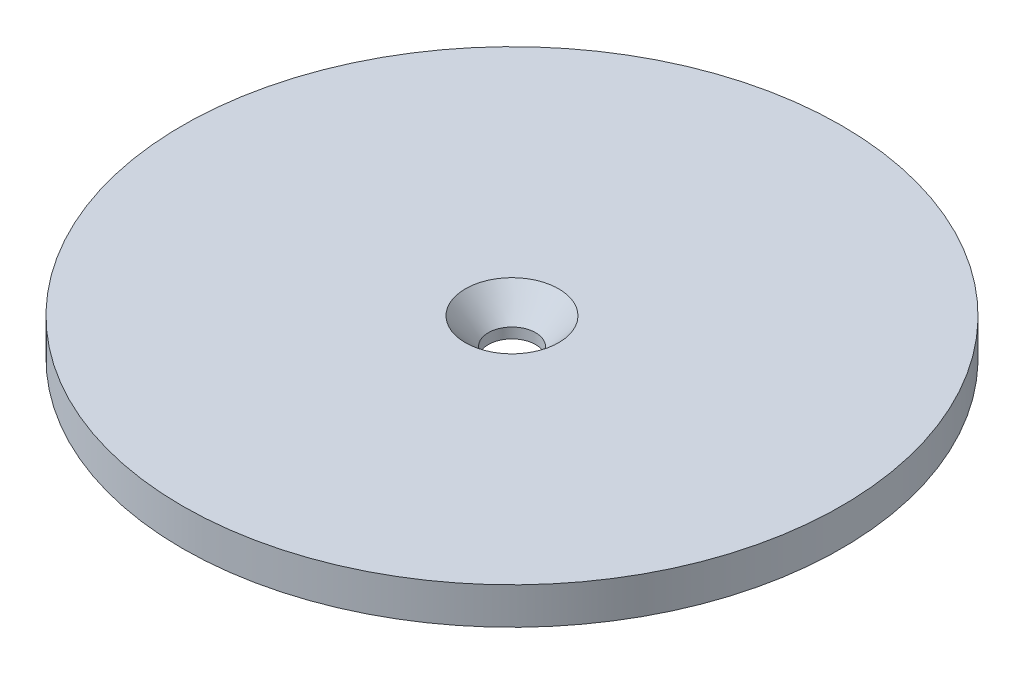
SolidWorks part; units mm, degrees
ref_plane "Front Plane" through (0, 0, 0) normal (0, 0, 1) x (1, 0, 0)
ref_plane "Top Plane" through (0, 0, 0) normal (0, 1, 0) x (1, 0, 0)
ref_plane "Right Plane" through (0, 0, 0) normal (1, 0, 0) x (0, 0, -1)
sketch "Sketch1" plane through (0, 0, 0) normal (0, 1, 0) x (1, 0, 0)
  circle A0 centre (0, 0) radius 20.066 construction
  circle A1 centre (0, 0) radius 45.466
  dimension "D1" = 25.4
extrude "Boss-Extrude1" add sketch "Sketch1" along normal blind 25.4
sketch "Sketch3" plane through (0, 0, 0) normal (0, -1, 0) x (1, 0, 0)
  circle A0 centre (0, 0) radius 20.32
extrude "Cut-Extrude1" cut sketch "Sketch3" against normal blind 12.7
hole_wizard "CSK for 1/4 Flat Head Machine Screw1" positions "Sketch6" profile "Sketch7" countersink size "1/4" standard "ANSI Inch"
sketch "Sketch6" plane through (0, 25.4, 0) normal (0, 1, 0) x (1, 0, 0)
  point P0 (0, 0)
sketch "Sketch7" plane through (0, 25.4, 0) normal (1, 0, 0) x (0, 0, 1)
  line L0 (0, 0) -> (0, 27.3611)
  line L1 (0, 27.3611) -> (3.2639, 25.4)
  line L2 (3.2639, 25.4) -> (3.2639, 3.6524)
  line L3 (3.2639, 3.6524) -> (6.4389, 0)
  line L5 (6.4389, 0) -> (0, 0)
  line L6 (-3.2639, 3.6524) -> (-6.4389, 0) construction
  line L10 (0, 27.3611) -> (-3.2639, 25.4) construction
  line L11 (0, -6.35) -> (0, 107.95) construction
  dimension "Hole Dia." = 6.5278
  dimension "Hole Depth" = 25.4
  dimension "Near C'Sink Dia." = 12.8778
  dimension "Near C'Sink Angle" = 82
  dimension "Drill Angle" = 118
sketch "Sketch9" plane through (0, 0, 0) normal (0, -1, 0) x (1, 0, 0)
  circle A0 centre (0, 0) radius 53.0319
extrude "Cut-Extrude3" cut sketch "Sketch9" against normal blind 20.3224
